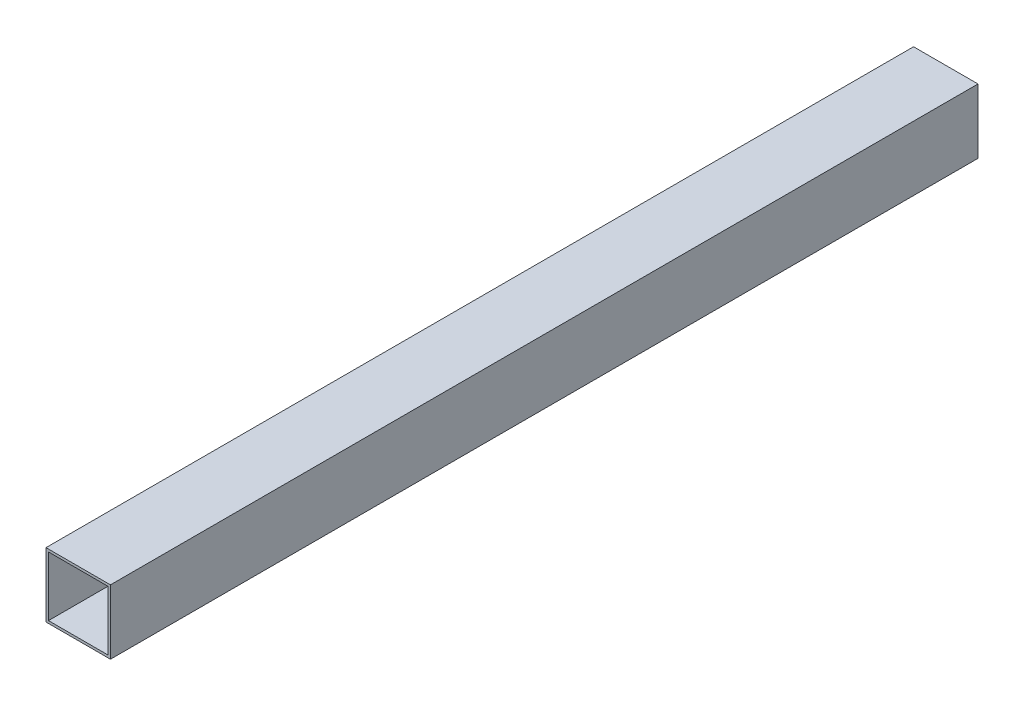
SolidWorks part; units mm, degrees
ref_plane "Front Plane" through (0, 0, 0) normal (0, 0, 1) x (1, 0, 0)
ref_plane "Top Plane" through (0, 0, 0) normal (0, 1, 0) x (1, 0, 0)
ref_plane "Right Plane" through (0, 0, 0) normal (1, 0, 0) x (0, 0, -1)
sketch "Sketch1" plane through (0, 0, 0) normal (0, 0, 1) x (1, 0, 0)
  line L5 (-36.576, 36.576) -> (36.576, 36.576)
  line L6 (-36.576, 36.576) -> (-36.576, -36.576)
  line L11 (-36.576, -36.576) -> (36.576, -36.576)
  line L12 (36.576, 36.576) -> (36.576, -36.576)
  line L13 (-36.576, 36.576) -> (36.576, -36.576) construction
  line L14 (-36.576, -36.576) -> (36.576, 36.576) construction
  line L15 (39.624, -39.624) -> (-39.624, -39.624)
  line L16 (39.624, -39.624) -> (39.624, 39.624)
  line L17 (39.624, 39.624) -> (-39.624, 39.624)
  line L18 (-39.624, -39.624) -> (-39.624, 39.624)
  line L19 (39.624, -39.624) -> (-39.624, 39.624) construction
  line L20 (39.624, 39.624) -> (-39.624, -39.624) construction
  point P0 (0, 0)
  point P6 (0, 0)
  dimension "D1" = 3.048
  dimension "D3" = 76.2
extrude "Boss-Extrude1" add sketch "Sketch1" along normal blind 1066.8
